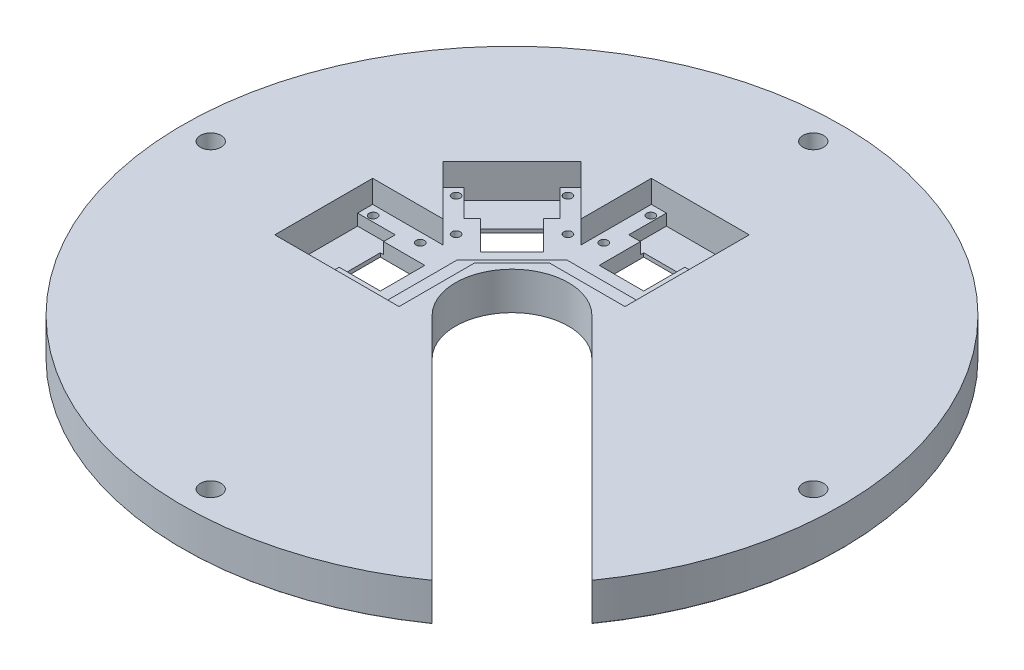
SolidWorks part; units mm, degrees
ref_plane "Front Plane" through (0, 0, 0) normal (0, 0, 1) x (1, 0, 0)
ref_plane "Top Plane" through (0, 0, 0) normal (0, 1, 0) x (1, 0, 0)
ref_plane "Right Plane" through (0, 0, 0) normal (1, 0, 0) x (0, 0, -1)
sketch "Sketch1" plane through (0, 0, 0) normal (0, 1, 0) x (1, 0, 0)
  circle A0 centre (0, 0) radius 87.5
  dimension "D1" = 175
extrude "Boss-Extrude1" add sketch "Sketch1" along normal blind 10
sketch "Sketch2" plane through (0, 10, 0) normal (0, 1, 0) x (1, 0, 0)
  circle A0 centre (0, -80) radius 7.5
  circle A1 centre (-80, 0) radius 7.5
  circle A2 centre (0, 80) radius 7.5
  circle A3 centre (80, 0) radius 7.5
  circle A4 centre (0, 0) radius 87.5 construction
  dimension "D1" = 15
extrude "Boss-Extrude2" add sketch "Sketch2" along normal blind 80
sketch "Sketch3" plane through (0, 0, 0) normal (0, -1, 0) x (-1, 0, 0)
  circle A0 centre (-80, 0) radius 7.5 construction
  circle A1 centre (0, 80) radius 7.5 construction
  circle A2 centre (80, 0) radius 7.5 construction
  circle A3 centre (0, -80) radius 7.5 construction
  point P0 (-80, 0)
  point P2 (0, 80)
  point P4 (80, 0)
  point P6 (0, -80)
hole_wizard "CBORE for M5 Hex Head Bolt1" positions "Sketch3" profile "Sketch4" counterbore size "M5" standard "ANSI Metric"
sketch "Sketch4" plane through (80, 0, 0) normal (1, 0, 0) x (0, 0, -1)
  line L0 (0, 0) -> (0, 21.6524)
  line L1 (0, 21.6524) -> (2.75, 20)
  line L2 (2.75, 20) -> (2.75, 3.58)
  line L3 (2.75, 3.58) -> (6.12, 3.58)
  line L5 (6.12, 3.58) -> (6.12, 0.025)
  line L6 (6.12, 0.025) -> (6.145, 0)
  line L7 (6.145, 0) -> (0, 0)
  line L8 (-6.12, 0.025) -> (-6.145, 0) construction
  line L10 (0, 21.6524) -> (-2.75, 20) construction
  line L11 (0, -6.35) -> (0, 107.95) construction
  dimension "Hole Dia." = 5.5
  dimension "Hole Depth" = 20
  dimension "C'Bore Dia." = 12.24
  dimension "C'Bore Depth" = 3.58
  dimension "Near C'Sink Dia." = 12.29
  dimension "Near C'Sink Angle" = 90
  dimension "Drill Angle" = 118
sketch "Sketch5" plane through (0, 10, 0) normal (0, 1, 0) x (1, 0, 0)
  circle A0 centre (0, 0) radius 87.5
  arc A1 (0, 87.5) -> (-87.5, 0) centre (0, 0) ccw construction
extrude "Cut-Extrude1" cut sketch "Sketch5" along normal blind 80
fillet "Fillet1" radius 0.1 1 edges at (0, 0, 87.5)
sketch "Sketch6" plane through (0, 10, 0) normal (0, 1, 0) x (1, 0, 0)
  line L0 (10.6066, 10.6066) -> (71.5625, -50.3493)
  line L1 (-10.6066, -10.6066) -> (50.3493, -71.5625)
  line L2 (0, -5.5) -> (0, 5.5) construction
  arc A0 (10.6066, 10.6066) -> (-10.6066, -10.6066) centre (0, 0) ccw
  circle A2 centre (0, 0) radius 87.5 construction
  arc A3 (50.3493, -71.5625) -> (71.5625, -50.3493) centre (0, 0) ccw
  dimension "D1" = 30
  dimension "D2" = 45
extrude "Cut-Extrude2" cut sketch "Sketch6" against normal blind 10
sketch "Sketch7" plane through (0, 10, 0) normal (0, 1, 0) x (1, 0, 0)
  line L5 (-8.4853, 26.8701) -> (-26.8701, 8.4853)
  line L10 (-26.8701, 8.4853) -> (-44.5477, 26.163)
  line L11 (-44.5477, 26.163) -> (-26.163, 44.5477)
  line L12 (-26.163, 44.5477) -> (-8.4853, 26.8701)
  line L13 (71.5625, -50.3493) -> (10.6066, 10.6066) construction
  dimension "D1" = 26
  dimension "D2" = 25
  dimension "D3" = 13
  dimension "D4" = 25
extrude "Cut-Extrude3" cut sketch "Sketch7" against normal blind 6
sketch "Sketch8" plane through (0, 0, 0) normal (0, -1, 0) x (1, 0, 0)
  line L0 (-24.7219, -16.378) -> (-16.378, -24.7219)
  line L1 (-16.378, -24.7219) -> (-24.7219, -33.0657)
  line L2 (-24.7219, -33.0657) -> (-33.0657, -24.7219)
  line L3 (-33.0657, -24.7219) -> (-24.7219, -16.378)
  line L4 (-24.7219, -17.0851) -> (-32.3586, -24.7219) construction
  line L5 (-17.0851, -24.7219) -> (-24.7219, -17.0851) construction
  line L6 (-24.7219, -32.3586) -> (-17.0851, -24.7219) construction
  line L7 (-32.3586, -24.7219) -> (-24.7219, -32.3586) construction
  dimension "D1" = 0.5
  dimension "D2" = 0.5
  dimension "D3" = 0.5
  dimension "D4" = 0.5
extrude "Cut-Extrude4" cut sketch "Sketch8" against normal blind 6
sketch "Sketch10" plane through (0, 4, 0) normal (0, 1, 0) x (1, 0, 0)
  line L0 (-41.7193, 28.9914) -> (-28.9914, 41.7193)
  line L5 (-28.9914, 41.7193) -> (-21.9203, 34.6482)
  line L7 (-21.9203, 34.6482) -> (-34.6482, 21.9203)
  line L9 (-34.6482, 21.9203) -> (-41.7193, 28.9914)
  line L10 (-44.5477, 26.163) -> (-26.8701, 8.4853) construction
  line L11 (-8.4853, 26.8701) -> (-26.163, 44.5477) construction
  line L12 (-26.163, 44.5477) -> (-44.5477, 26.163) construction
  dimension "D1" = 10
  dimension "D2" = 4
  dimension "D3" = 4
extrude "Cut-Extrude5" cut sketch "Sketch10" against normal blind 3
sketch "Sketch11" plane through (0, 4, 0) normal (0, 1, 0) x (1, 0, 0)
  circle A0 centre (-26.0654, 40.9146) radius 1.1 construction
  circle A1 centre (-40.9146, 26.0654) radius 1.1 construction
  circle A2 centre (-32.0758, 17.2265) radius 1.1 construction
  circle A3 centre (-17.2265, 32.0758) radius 1.1 construction
  circle A4 centre (-26.0654, 40.9146) radius 1.1
  circle A5 centre (-40.9146, 26.0654) radius 1.1
  circle A6 centre (-32.0758, 17.2265) radius 1.1
  circle A7 centre (-17.2265, 32.0758) radius 1.1
extrude "Cut-Extrude6" cut sketch "Sketch11" against normal blind 10
sketch "Sketch12" plane through (0, 10, 0) normal (0, 1, 0) x (1, 0, 0)
  line L0 (-26.8701, 8.4853) -> (-8.4853, 26.8701)
  line L1 (-8.4853, 26.8701) -> (-2.8284, 21.2132)
  line L2 (-2.8284, 21.2132) -> (-21.2132, 2.8284)
  line L3 (-21.2132, 2.8284) -> (-26.8701, 8.4853)
  dimension "D1" = 8
extrude "Cut-Extrude7" cut sketch "Sketch12" against normal blind 5
pattern_circular "CirPattern1" count 2 every 45 about axis through (0, 0, 0) along (0, 1, 0) of "Cut-Extrude3", "Cut-Extrude4", "Cut-Extrude5", "Cut-Extrude6", "Cut-Extrude7"
